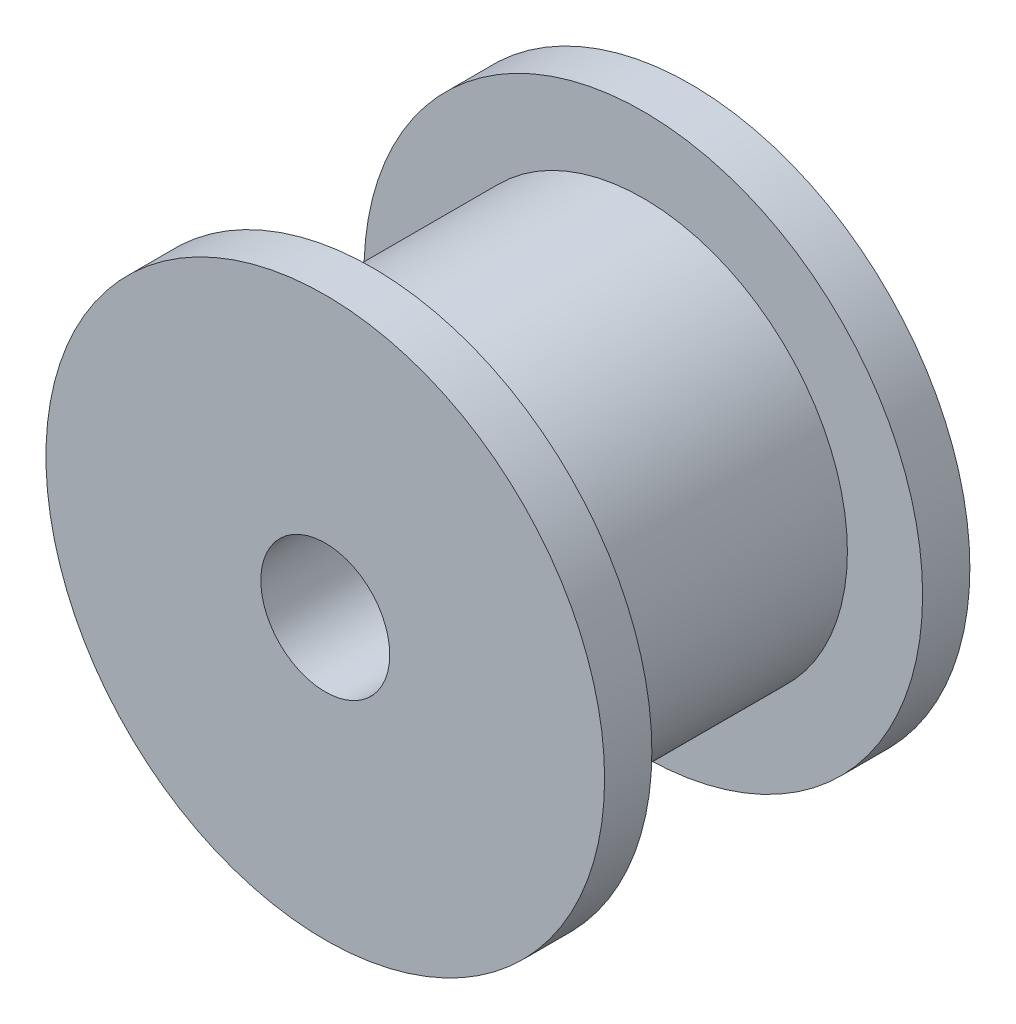
SolidWorks part; units mm, degrees
ref_plane "前视基准面" through (0, 0, 0) normal (0, 0, 1) x (1, 0, 0)
ref_plane "上视基准面" through (0, 0, 0) normal (0, 1, 0) x (1, 0, 0)
ref_plane "右视基准面" through (0, 0, 0) normal (1, 0, 0) x (0, 0, -1)
sketch "草图1" plane through (0, 0, 0) normal (0, 0, 1) x (1, 0, 0)
  circle A0 centre (0, 0) radius 6.5
  dimension "D1" = 13
extrude "凸台-拉伸1" add sketch "草图1" along normal blind 8.5
sketch "草图2" plane through (0, 0, 8.5) normal (0, 0, 1) x (1, 0, 0)
  circle A0 centre (0, 0) radius 1.5
  dimension "D1" = 3
extrude "切除-拉伸1" cut sketch "草图2" against normal blind 10
ref_plane "基准面1" through (0, 0, 7.4) normal (0, 0, 1) x (1, 0, 0)
sketch "草图3" plane through (0, 0, 7.4) normal (0, 0, 1) x (1, 0, 0)
  circle A0 centre (0, 0) radius 4.75
  circle A1 centre (0, 0) radius 9
  dimension "D1" = 9.5
  dimension "D2" = 18
extrude "切除-拉伸2" cut sketch "草图3" against normal blind 6.3
